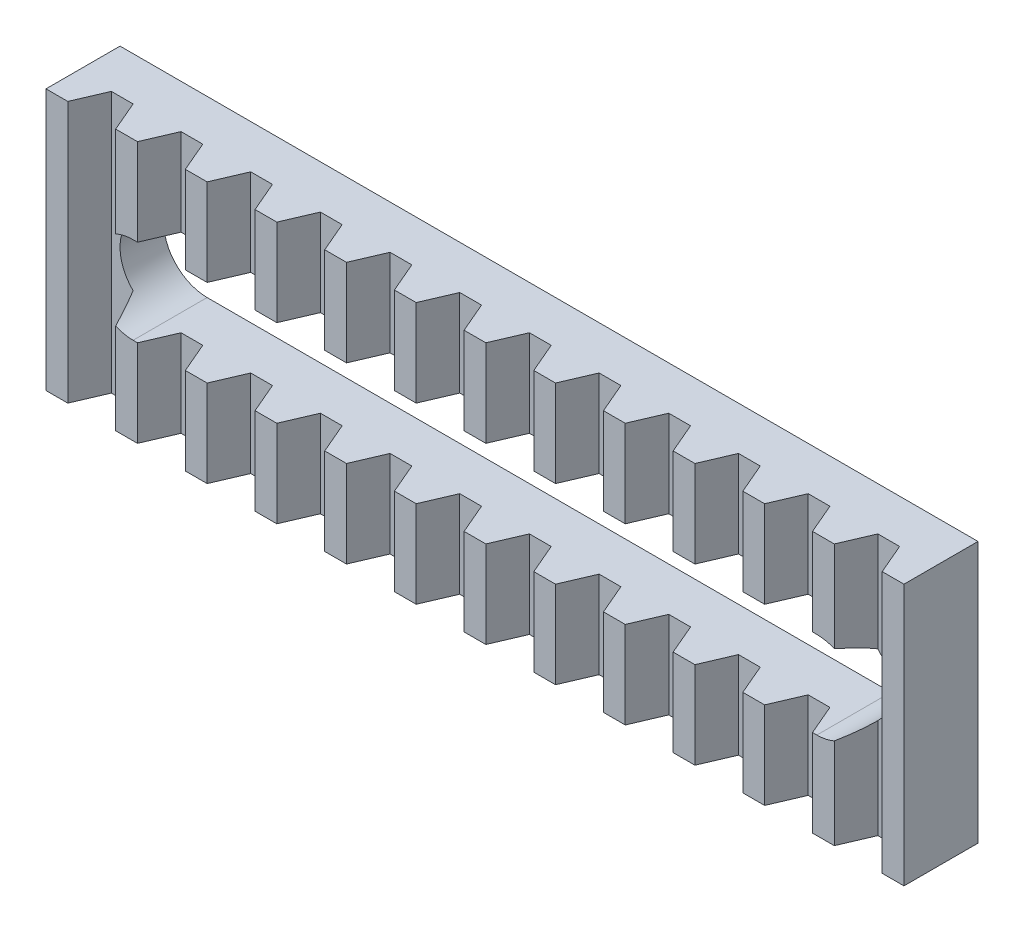
SolidWorks part; units mm, degrees
ref_plane "Front" through (0, 0, 0) normal (0, 0, 1) x (1, 0, 0)
ref_plane "Top" through (0, 0, 0) normal (0, 1, 0) x (1, 0, 0)
ref_plane "Right" through (0, 0, 0) normal (1, 0, 0) x (0, 0, -1)
sketch "Sketch1" plane through (0, 0, 0) normal (0, 1, 0) x (1, 0, 0)
  line L0 (-98.5, 0) -> (98.5, 0)
  line L1 (-98.5, 0) -> (-98.5, -17)
  line L2 (-98.5, -17) -> (-93.5, -17)
  line L3 (-93.5, -17) -> (-90.5, -10)
  line L4 (-90.5, -10) -> (-85.5, -10)
  line L5 (-85.5, -10) -> (-82.5, -17)
  line L6 (-82.5, -17) -> (-77.5, -17)
  line L7 (-77.5, -17) -> (-74.5, -10)
  line L8 (-74.5, -10) -> (-69.5, -10)
  line L9 (-69.5, -10) -> (-66.5, -17)
  line L10 (-66.5, -17) -> (-61.5, -17)
  line L11 (-61.5, -17) -> (-58.5, -10)
  line L12 (-58.5, -10) -> (-53.5, -10)
  line L13 (-53.5, -10) -> (-50.5, -17)
  line L14 (-50.5, -17) -> (-45.5, -17)
  line L15 (-45.5, -17) -> (-42.5, -10)
  line L16 (-42.5, -10) -> (-37.5, -10)
  line L17 (-37.5, -10) -> (-34.5, -17)
  line L18 (-34.5, -17) -> (-29.5, -17)
  line L19 (-29.5, -17) -> (-26.5, -10)
  line L20 (-26.5, -10) -> (-21.5, -10)
  line L21 (-21.5, -10) -> (-18.5, -17)
  line L22 (-18.5, -17) -> (-13.5, -17)
  line L23 (-13.5, -17) -> (-10.5, -10)
  line L24 (-10.5, -10) -> (-5.5, -10)
  line L25 (-5.5, -10) -> (-2.5, -17)
  line L26 (-2.5, -17) -> (2.5, -17)
  line L27 (2.5, -17) -> (5.5, -10)
  line L28 (5.5, -10) -> (10.5, -10)
  line L29 (10.5, -10) -> (13.5, -17)
  line L30 (13.5, -17) -> (18.5, -17)
  line L31 (18.5, -17) -> (21.5, -10)
  line L32 (21.5, -10) -> (26.5, -10)
  line L33 (26.5, -10) -> (29.5, -17)
  line L34 (29.5, -17) -> (34.5, -17)
  line L35 (34.5, -17) -> (37.5, -10)
  line L36 (37.5, -10) -> (42.5, -10)
  line L37 (42.5, -10) -> (45.5, -17)
  line L38 (45.5, -17) -> (50.5, -17)
  line L39 (50.5, -17) -> (53.5, -10)
  line L40 (53.5, -10) -> (58.5, -10)
  line L41 (58.5, -10) -> (61.5, -17)
  line L42 (61.5, -17) -> (66.5, -17)
  line L43 (66.5, -17) -> (69.5, -10)
  line L44 (69.5, -10) -> (74.5, -10)
  line L45 (74.5, -10) -> (77.5, -17)
  line L46 (77.5, -17) -> (82.5, -17)
  line L47 (82.5, -17) -> (85.5, -10)
  line L48 (85.5, -10) -> (90.5, -10)
  line L49 (90.5, -10) -> (93.5, -17)
  line L50 (93.5, -17) -> (98.5, -17)
  line L51 (98.5, -17) -> (98.5, 0)
  dimension "D1" = 197
  dimension "D2" = 98.5
  dimension "D3" = 10
  dimension "D4" = 7
  dimension "D5" = 5
  dimension "D6" = 5
  dimension "D7" = 3
  dimension "D8" = 3
  dimension "D10" = 5
  dimension "D9" = 12
extrude "Boss-Extrude1" add sketch "Sketch1" along normal blind 60 contours L50 L51 L0 L1 L2 L3 L4 L5 L6 L7 L8 L9 L10 L11 L12 L13 L14 L15 L16 L17 L18 L19 L20 L21 L22 L23 L24 L25 L26 L27 L28 L29 L30 L31 L32 L33 L34 L35 L36 L37 L38 L39 L40 L41 L42 L43 L44 L45 L46 L47 L48
sketch "Sketch2" plane through (0, 0, 0) normal (0, 0, 1) x (1, 0, 0)
  line L0 (0, -21.2611) -> (0, 75.6496) construction
  line L1 (-78.5, 40) -> (78.5, 40)
  line L2 (-78.5, 20) -> (78.5, 20)
  line L3 (13.5, 60) -> (18.5, 60) construction
  line L4 (-98.5, 60) -> (-98.5, 0) construction
  line L5 (98.5, 60) -> (98.5, 0) construction
  arc A0 (-78.5, 40) -> (-78.5, 20) centre (-78.5, 30) ccw
  arc A1 (78.5, 20) -> (78.5, 40) centre (78.5, 30) ccw
  point P11 (-98.5, 30)
  point P14 (98.5, 30)
  dimension "D3" = 10
  dimension "D4" = 10
  dimension "D6" = 20
  dimension "D1" = 20
  dimension "D2" = 20
  dimension "D5" = 20
extrude "Cut-Extrude1" cut sketch "Sketch2" against normal mid plane 60
ref_point "Point1"
ref_point "Point2"
